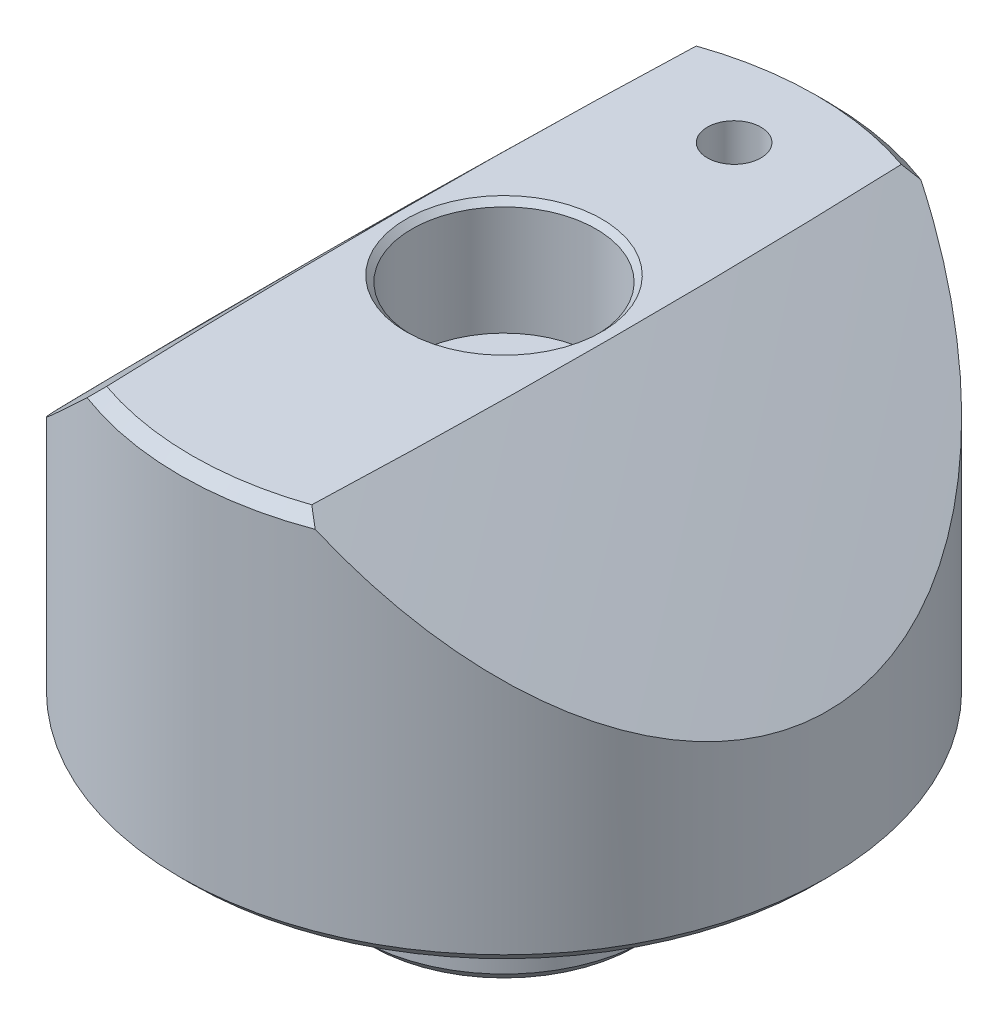
SolidWorks part; units mm, degrees
material "440C Rc 58"
ref_plane "Front Plane" through (0, 0, 0) normal (0, 0, 1) x (1, 0, 0)
ref_plane "Top Plane" through (0, 0, 0) normal (0, 1, 0) x (1, 0, 0)
ref_plane "Right Plane" through (0, 0, 0) normal (1, 0, 0) x (0, 0, -1)
sketch "Sketch1" plane through (0, 0, 0) normal (0, 1, 0) x (1, 0, 0)
  circle A0 centre (0, 0) radius 14.2875
  dimension "D1" = 28.575
extrude "Boss-Extrude1" add sketch "Sketch1" along normal blind 16.383
sketch "Sketch2" plane through (0, 0, 0) normal (0, -1, 0) x (1, 0, 0)
  circle A0 centre (0, 0) radius 6.35
  dimension "D1" = 12.7
extrude "Boss-Extrude2" add sketch "Sketch2" along normal blind 6.35
sketch "Sketch4" plane through (0, 16.383, 0) normal (0, 1, 0) x (1, 0, 0)
  line L0 (0, 0) -> (0, 10.16) construction
  circle A0 centre (0, 10.16) radius 1.1811
  dimension "D2" = 2.3622
  dimension "D1" = 10.16
extrude "Cut-Extrude1" cut sketch "Sketch4" against normal through all
chamfer "Chamfer1" distance 0.508 angle 45 3 edges at (0, -6.35, -6.35) (0, 0, 14.2875) (0, 16.383, 14.2875)
sketch "Sketch5" plane through (0, 0, 0) normal (0, 0, 1) x (1, 0, 0)
  line L0 (-2.5484, 18.669) -> (-16.0887, 5.1287)
  line L1 (-2.5484, 18.669) -> (2.5484, 18.669)
  line L2 (2.5484, 18.669) -> (16.0887, 5.1287)
  line L3 (16.0887, 5.1287) -> (16.0887, 23.8274)
  line L4 (16.0887, 23.8274) -> (-16.0887, 23.8274)
  line L5 (-16.0887, 23.8274) -> (-16.0887, 5.1287)
extrude "Cut-Extrude2" cut sketch "Sketch5" against normal mid plane 37.846
sketch "Sketch6" plane through (0, 0, 0) normal (0, 0, 1) x (1, 0, 0)
  line L0 (-4.8344, 16.383) -> (-14.2875, 6.9299) construction
  line L1 (-9.5609, 11.6564) -> (343.9917, -341.8962) construction
  line L2 (343.9917, -341.8962) -> (343.9917, 49658.1038) construction
  line L4 (0.6045, 21.5377) -> (-20.7774, 21.5377)
  line L5 (-20.7774, 21.5377) -> (-20.7774, 0.0723)
  arc A0 (-20.7774, 0.0723) -> (0.6045, 21.5377) centre (343.9917, -341.8962) cw
  dimension "D4" = 499.999
  dimension "D1" = 499.999
  dimension "D2" = 20.7774
  dimension "D3" = 21.5377
revolve "Cut-Revolve1" cut sketch "Sketch6" angle 5 mid plane about L2
mirror "Mirror1" about plane through (0, 0, 0) normal (1, 0, 0) of "Cut-Revolve1"
sketch "Sketch7" plane through (0, 0, 0) normal (0, 0, 1) x (1, 0, 0)
  line L0 (6.799, -0.449) -> (6.799, 0) construction
  line L1 (-13.7795, 0) -> (13.7795, 0) construction
  line L2 (6.799, -0.449) -> (6.35, -0.449) construction
  line L3 (6.35, -5.842) -> (6.35, 0) construction
  circle A0 centre (6.799, -0.449) radius 0.635
  point P2 (6.35, 0)
  dimension "D1" = 1.27
revolve "Cut-Revolve2" cut sketch "Sketch7" angle 360 about axis through (0, 16.383, 0) along (0, -1, 0)
hole_wizard "1/4-20 Tapped Hole1" positions "Sketch9" profile "Sketch8" tap size "1/4-20" standard "ANSI Inch" end condition through all
sketch "Sketch9" plane through (0, 16.383, 0) normal (0, 1, 0) x (1, 0, 0)
  point P0 (0, 0)
cosmetic thread "Hole Thread1" parameters "D2"=6.35
sketch "Sketch8" plane through (0, 16.383, 0) normal (1, 0, 0) x (0, 0, 1)
  line L0 (0, 0) -> (0, 22.733)
  line L1 (0, 22.733) -> (2.5527, 22.733)
  line L2 (2.5527, 22.733) -> (2.5527, 0)
  line L5 (2.5527, 0) -> (0, 0)
  line L11 (0, -6.35) -> (0, 107.95) construction
  dimension "Thru Tap Drill Dia." = 5.1054
  dimension "Thru Tap Drill Depth" = 22.733
hole_wizard "Hole1" positions "Sketch12" profile "Sketch11" legacy
sketch "Sketch12" plane through (0, 16.383, 0) normal (0, 1, 0) x (1, 0, 0)
  point P0 (0, 0)
sketch "Sketch11" plane through (0, 16.383, 0) normal (1, 0, 0) x (0, 0, 1)
  line L0 (0, 0) -> (0, 5.08)
  line L1 (0, 5.08) -> (4.064, 5.08)
  line L2 (4.064, 5.08) -> (4.064, 0)
  line L3 (4.064, 0) -> (0, 0)
  line L4 (0, 110) -> (0, -10) construction
  dimension "Diameter" = 8.128
  dimension "Depth" = 5.08
chamfer "Chamfer2" distance 0.254 angle 45 3 edges at (0, 11.303, -2.5527) (0, -6.35, 2.5527) (0, 16.383, 4.064)
sketch "Tangent point of contact with VB height" plane through (0, 0, 0) normal (0, 0, 1) x (1, 0, 0)
  line L0 (-9.5609, 11.6564) -> (-50009.5609, 11.6564) construction
